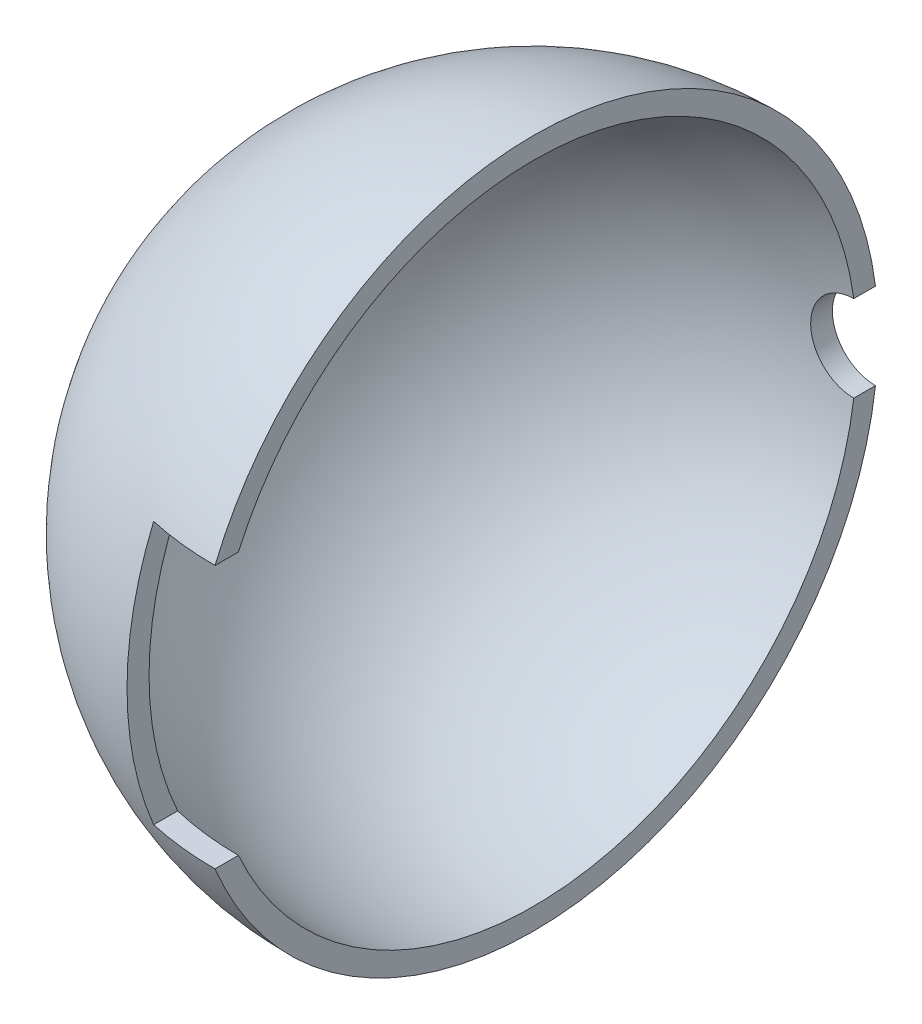
SolidWorks part; units mm, degrees
ref_plane "Front Plane" through (0, 0, 0) normal (0, 0, 1) x (1, 0, 0)
ref_plane "Top Plane" through (0, 0, 0) normal (0, 1, 0) x (1, 0, 0)
ref_plane "Right Plane" through (0, 0, 0) normal (1, 0, 0) x (0, 0, -1)
sketch "Sketch1" plane through (0, 0, 0) normal (0, 0, 1) x (1, 0, 0)
  line L0 (0, 8) -> (0, 7.5)
  line L1 (-8, 0) -> (-7.5, 0)
  arc A0 (0, 8) -> (-8, 0) centre (0, 0) ccw
  arc A1 (0, 7.5) -> (-7.5, 0) centre (0, 0) ccw
  dimension "D1" = 8
  dimension "D2" = 0.5
revolve "Revolve1" add sketch "Sketch1" angle 360 about L1
ref_plane "Plane1" through (0, 0, 8) normal (0, 0, 1) x (1, 0, 0)
sketch "Sketch2" plane through (0, 0, 8) normal (0, 0, 1) x (1, 0, 0)
  line L1 (-1.6, -3.05) -> (1.6, -3.05)
  line L2 (-1.6, -3.05) -> (-1.6, 3.05)
  line L3 (-1.6, 3.05) -> (1.6, 3.05)
  line L4 (1.6, -3.05) -> (1.6, 3.05)
  line L5 (-1.6, -3.05) -> (1.6, 3.05) construction
  line L6 (-1.6, 3.05) -> (1.6, -3.05) construction
  point P0 (0, 0)
  dimension "D1" = 3.2
  dimension "D2" = 6.1
extrude "Cut-Extrude1" cut sketch "Sketch2" against normal blind 2
ref_plane "Plane2" through (0, 0, -8) normal (0, 0, 1) x (1, 0, 0)
sketch "Sketch3" plane through (0, 0, -8) normal (0, 0, 1) x (1, 0, 0)
  circle A0 centre (0, 0) radius 1
  dimension "D1" = 2
extrude "Cut-Extrude2" cut sketch "Sketch3" along normal up to surface (0.567 mm away)
